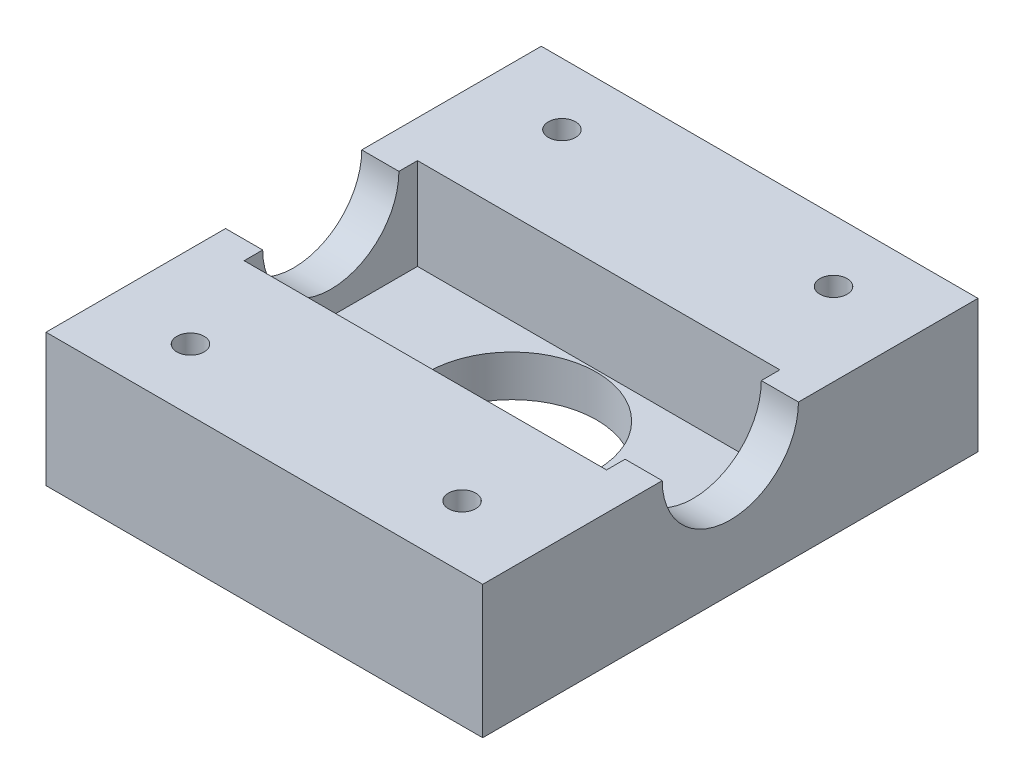
SolidWorks part; units mm, degrees
material "1060 Alloy"
ref_plane "Front Plane" through (0, 0, 0) normal (0, 0, 1) x (1, 0, 0)
ref_plane "Top Plane" through (0, 0, 0) normal (0, 1, 0) x (1, 0, 0)
ref_plane "Right Plane" through (0, 0, 0) normal (1, 0, 0) x (0, 0, -1)
sketch "Sketch1" plane through (0, 0, 0) normal (0, 1, 0) x (1, 0, 0)
  line L1 (-26.45, 15) -> (26.45, 15)
  line L2 (-26.45, 15) -> (-26.45, -15)
  line L3 (-26.45, -15) -> (26.45, -15)
  line L4 (26.45, 15) -> (26.45, -15)
  line L5 (-26.45, 15) -> (26.45, -15) construction
  line L6 (-26.45, -15) -> (26.45, 15) construction
  circle A0 centre (0, 0) radius 10.25
  point P0 (0, 0)
  dimension "D3" = 20.5
  dimension "D1" = 52.9
  dimension "D2" = 30
extrude "Boss-Extrude1" add sketch "Sketch1" along normal blind 5
sketch "Sketch3" plane through (0, 5, 0) normal (0, 1, 0) x (1, 0, 0)
  line L0 (-21.95, -10.5) -> (21.95, -10.5)
  line L1 (-26.45, 15) -> (26.45, 15)
  line L2 (-26.45, 15) -> (-26.45, -15)
  line L3 (-26.45, -15) -> (26.45, -15)
  line L4 (26.45, 15) -> (26.45, -15)
  line L5 (21.95, 10.5) -> (21.95, -10.5)
  line L6 (-21.95, 10.5) -> (21.95, 10.5)
  line L7 (-21.95, 10.5) -> (-21.95, -10.5)
  dimension "D1" = 4.5
extrude "Boss-Extrude2" add sketch "Sketch3" along normal blind 11.1
sketch "Sketch4" plane through (26.45, 0, 0) normal (1, 0, 0) x (0, 0, -1)
  line L0 (-15, 16.1) -> (15, 16.1) construction
  circle A0 centre (0, 16.1) radius 8.25
  dimension "D1" = 16.5
extrude "Cut-Extrude1" cut sketch "Sketch4" against normal through all
sketch "Sketch5" plane through (0, 0, 15) normal (0, 0, 1) x (1, 0, 0)
  line L0 (26.45, 16.1) -> (26.45, 0) construction
  line L1 (-26.45, 16.1) -> (26.45, 16.1)
  line L2 (-26.45, 16.1) -> (-26.45, 11.1)
  line L3 (-26.45, 11.1) -> (26.45, 11.1)
  line L4 (26.45, 16.1) -> (26.45, 11.1)
  dimension "D1" = 5
sketch "Sketch6" plane through (0, 0, -15) normal (0, 0, -1) x (-1, 0, 0)
  line L0 (26.45, 16.1) -> (26.45, 0) construction
  line L1 (-26.45, 16.1) -> (26.45, 16.1)
  line L2 (-26.45, 16.1) -> (-26.45, 11.1)
  line L3 (-26.45, 11.1) -> (26.45, 11.1)
  line L4 (26.45, 16.1) -> (26.45, 11.1)
  dimension "D1" = 5
extrude "Boss-Extrude3" add sketch "Sketch5" along normal blind 15
extrude "Boss-Extrude4" add sketch "Sketch6" along normal blind 15
sketch "Sketch7" plane through (0, 11.1, 0) normal (0, -1, 0) x (1, 0, 0)
  line L1 (26.45, 15) -> (-26.45, 15)
  line L2 (26.45, 15) -> (26.45, 30)
  line L3 (26.45, 30) -> (-26.45, 30)
  line L4 (-26.45, 15) -> (-26.45, 30)
  line L5 (-26.45, -15) -> (26.45, -15)
  line L6 (-26.45, -15) -> (-26.45, -30)
  line L7 (-26.45, -30) -> (26.45, -30)
  line L8 (26.45, -15) -> (26.45, -30)
extrude "Boss-Extrude5" add sketch "Sketch7" along normal up to surface (11.1 mm away) up to face at (0, 0, 0)
sketch "Sketch8" plane through (0, 16.1, 0) normal (0, 1, 0) x (1, 0, 0)
  line L0 (26.45, -30) -> (-26.45, -30) construction
  line L1 (-26.45, -8.25) -> (-26.45, -30) construction
  line L2 (-26.45, 30) -> (26.45, 30) construction
  line L3 (26.45, 8.25) -> (26.45, 30) construction
  circle A0 centre (-16.45, 22.5) radius 2
  circle A1 centre (16.45, 22.5) radius 2
  circle A2 centre (16.45, -22.5) radius 2
  circle A3 centre (-16.45, -22.5) radius 2
  dimension "D1" = 7.5
  dimension "D2" = 10
  dimension "D3" = 7.5
  dimension "D4" = 10
  dimension "D5" = 4
  dimension "D6" = 4
  dimension "D7" = 4
  dimension "D8" = 4
hole_wizard "M4 Tapped Hole1" positions "Sketch9" profile "Sketch10" tap size "M4" standard "ISO"
sketch "Sketch9" plane through (0, 16.1, 0) normal (0, 1, 0) x (1, 0, 0)
  point P0 (-16.45, -22.5)
  point P3 (16.45, -22.5)
  point P6 (16.45, 22.5)
  point P9 (-16.45, 22.5)
sketch "Sketch10" plane through (-16.45, 16.1, 22.5) normal (1, 0, 0) x (0, 0, 1)
  line L0 (0, 0) -> (0, 10.1)
  line L1 (0, 10.1) -> (1.65, 9.1086)
  line L2 (1.65, 9.1086) -> (1.65, 0)
  line L5 (1.65, 0) -> (0, 0)
  line L10 (0, 10.1) -> (-1.65, 9.1086) construction
  line L11 (0, -6.35) -> (0, 107.95) construction
  dimension "Tap Drill Dia." = 3.3
  dimension "Tap Drill Depth" = 10.1
  dimension "Drill Angle" = 118
cosmetic thread "Hole Thread1" parameters "D1"=8, "D2"=4
cosmetic thread "Hole Thread2" parameters "D1"=8, "D2"=4
cosmetic thread "Hole Thread3" parameters "D1"=8, "D2"=4
cosmetic thread "Hole Thread4" parameters "D1"=8, "D2"=4
